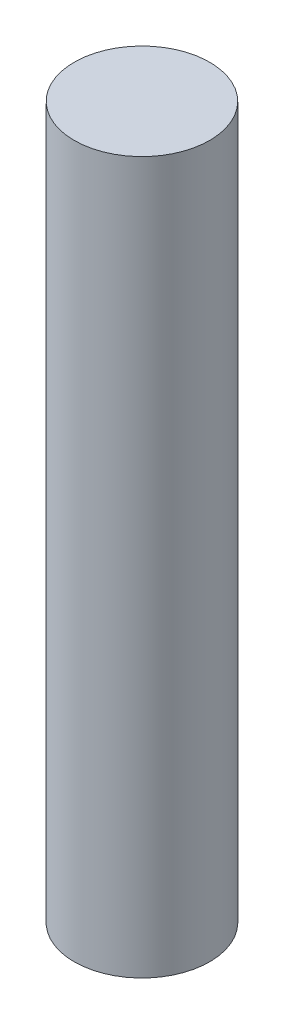
SolidWorks part; units mm, degrees
material "6061 Alloy"
ref_plane "Front Plane" through (0, 0, 0) normal (0, 0, 1) x (1, 0, 0)
ref_plane "Top Plane" through (0, 0, 0) normal (0, 1, 0) x (1, 0, 0)
ref_plane "Right Plane" through (0, 0, 0) normal (1, 0, 0) x (0, 0, -1)
sketch "Sketch1" plane through (0, 0, 0) normal (0, 1, 0) x (1, 0, 0)
  circle A0 centre (0, 0) radius 2
  dimension "D1" = 4
extrude "Boss-Extrude1" add sketch "Sketch1" along normal blind 21
